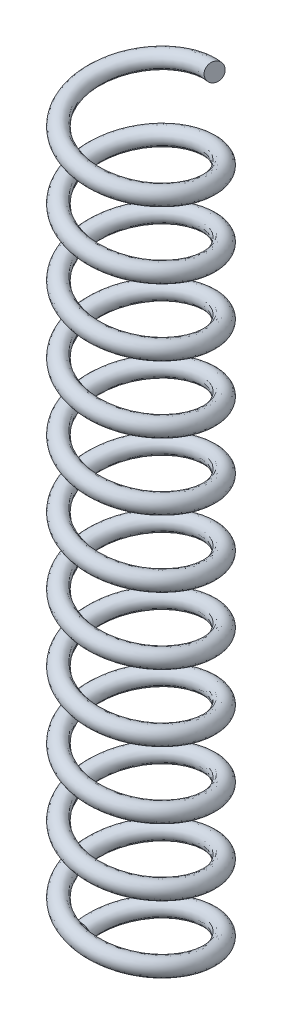
SolidWorks part; units mm, degrees
ref_plane "Front Plane" through (0, 0, 0) normal (0, 0, 1) x (1, 0, 0)
ref_plane "Top Plane" through (0, 0, 0) normal (0, 1, 0) x (1, 0, 0)
ref_plane "Right Plane" through (0, 0, 0) normal (1, 0, 0) x (0, 0, -1)
sketch "Sketch1" plane through (0, 0, 0) normal (0, 1, 0) x (1, 0, 0)
  circle A0 centre (0, 0) radius 1.75
  dimension "D1" = 3.5
curve "Helix/Spiral1" pitch 2 height 22.6 turns 11.3
sweep "Sweep1" add path "Helix/Spiral1" circular profile diameter 0.5 parameters "D3"=0.5
